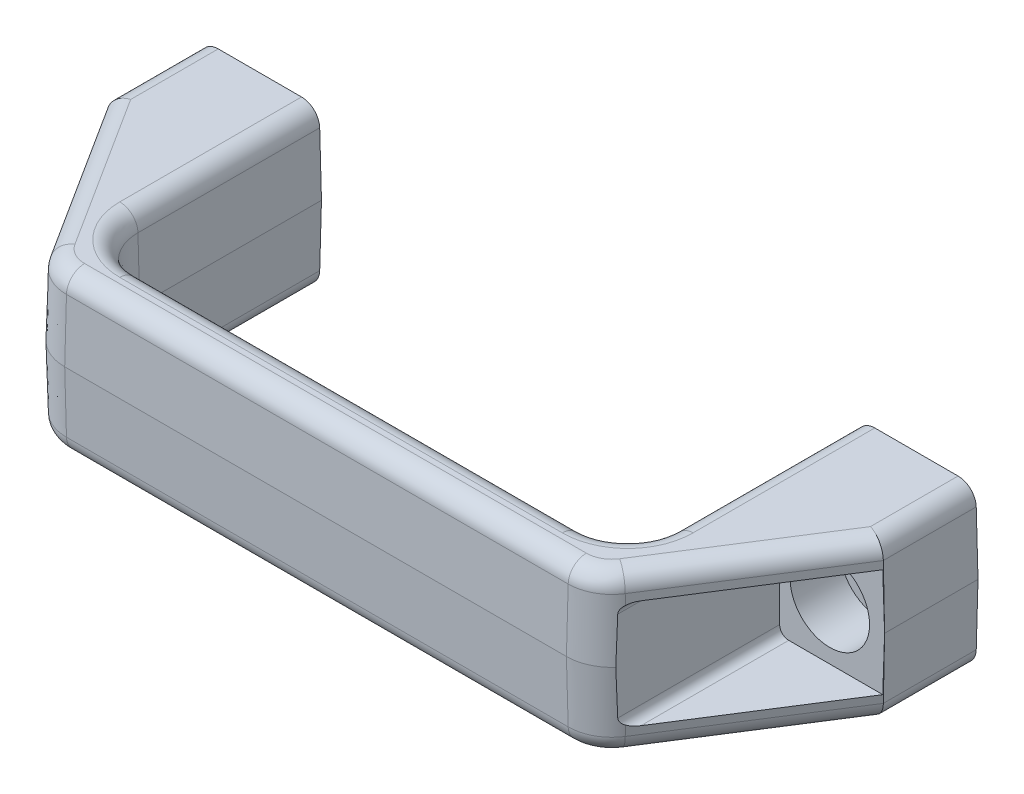
SolidWorks part; units mm, degrees
ref_plane "Front Plane" through (0, 0, 0) normal (0, 0, 1) x (1, 0, 0)
ref_plane "Top Plane" through (0, 0, 0) normal (0, 1, 0) x (1, 0, 0)
ref_plane "Right Plane" through (0, 0, 0) normal (1, 0, 0) x (0, 0, -1)
sketch "Sketch1" plane through (0, 0, 0) normal (0, 0, 1) x (1, 0, 0)
  line L0 (-46.8312, 0) -> (46.8312, 0)
  line L1 (0, 11.1125) -> (0, -11.1125)
  line L2 (-3, -11.1125) -> (3, -11.1125)
  point P4 (0, 0)
  point P8 (0, 0)
  point P10 (0, -11.1125)
sketch "Sketch2" plane through (0, 0, 0) normal (0, 1, 0) x (1, 0, 0)
  line L0 (0, 0) -> (0, -38.1)
  line L1 (0, -38.1) -> (0, -31.75)
  line L2 (-54.483, 0) -> (54.483, 0)
  point P7 (0, 0)
sketch "Sketch3" plane through (0, 0, 0) normal (0, 1, 0) x (1, 0, 0)
  line L0 (-30.9253, -31.75) -> (30.9253, -31.75)
  line L1 (37.2752, -25.4) -> (37.2752, 0)
  line L2 (-46.8312, 0) -> (46.8312, 0) construction
  line L3 (37.2752, 0) -> (54.483, 0)
  line L4 (54.483, 0) -> (54.483, -13.0556)
  line L5 (54.483, -13.0556) -> (40.4167, -35.1592)
  line L6 (35.0595, -38.1) -> (-35.0595, -38.1)
  line L7 (-40.4167, -35.1592) -> (-54.483, -13.0556)
  line L8 (-54.483, -13.0556) -> (-54.483, 0)
  line L9 (-54.483, 0) -> (-37.2752, 0)
  line L10 (-37.2752, 0) -> (-37.2752, -25.4)
  line L11 (0, 0) -> (0, -31.75) construction
  arc A0 (37.2752, -25.4) -> (30.9253, -31.75) centre (30.9253, -25.4) cw
  arc A1 (-30.9253, -31.75) -> (-37.2752, -25.4) centre (-30.9253, -25.4) cw
  arc A2 (-35.0595, -38.1) -> (-40.4167, -35.1592) centre (-35.0595, -31.75) cw
  arc A3 (35.0595, -38.1) -> (40.4167, -35.1592) centre (35.0595, -31.75) ccw
  point P17 (37.2752, -31.75)
  point P20 (-37.2752, -31.75)
  point P23 (-38.5453, -38.1)
  point P26 (38.5452, -38.1)
  dimension "D11" = 6.35
  dimension "D12" = 6.35
  dimension "D13" = 6.35
  dimension "D1" = 38.1
  dimension "D2" = 6.35
  dimension "D5" = 1.27
  dimension "D6" = 1.27
  dimension "D7" = 13.0556
  dimension "D8" = 13.0556
  dimension "D3" = 74.5505
extrude "Boss-Extrude1" add sketch "Sketch3" along normal up to vertex (11.1125 mm away) from vertex at -11.1125 starting at point (0, -11.1125, 0)
sketch "Sketch4" plane through (0, 0, 0) normal (1, 0, 0) x (0, 0, -1)
  line L0 (-38.1, 0) -> (-37.7825, 11.1125)
  line L1 (-38.1, 11.1125) -> (-38.1, -11.1125) construction
  line L2 (-35.1592, 11.1125) -> (-38.1, 11.1125) construction
  line L5 (-37.7825, 11.1125) -> (-38.1, 11.1125)
  line L6 (-38.1, 11.1125) -> (-38.1, 0)
  dimension "D1" = 0.3175
sketch "Sketch5" plane through (0, 0, 0) normal (0, 1, 0) x (1, 0, 0)
  line L0 (-54.483, 0) -> (-54.483, -13.0556)
  line L1 (54.483, -13.0556) -> (40.4167, -35.1592)
  line L2 (54.483, 0) -> (54.483, -13.0556)
  line L3 (-54.483, -13.0556) -> (-40.4167, -35.1592)
  line L4 (-35.0595, -38.1) -> (35.0595, -38.1)
  arc A0 (35.0595, -38.1) -> (40.4167, -35.1592) centre (35.0595, -31.75) ccw
  arc A1 (-35.0595, -38.1) -> (-40.4167, -35.1592) centre (-35.0595, -31.75) cw
  dimension "D4" = 13.0556
sweep "Cut-Sweep1" cut profiles "Sketch4" path "Sketch5"
mirror "Mirror1" about plane through (0, 0, 0) normal (0, 1, 0) of "Cut-Sweep1"
ref_plane "Plane1" through (0, 0, 13.0556) normal (0, 0, 1) x (1, 0, 0)
sketch "Sketch6" plane through (0, 0, 13.0556) normal (0, 0, 1) x (1, 0, 0)
  line L1 (-54.483, 7.5565) -> (-41.0853, 7.5565)
  line L2 (-54.483, 7.5565) -> (-54.483, -7.5565)
  line L3 (-54.483, -7.5565) -> (-41.0853, -7.5565)
  line L4 (-39.8152, 6.2865) -> (-39.8152, -6.2865)
  line L7 (54.1655, 11.1125) -> (37.2752, 11.1125) construction
  line L8 (54.483, 7.5565) -> (41.0852, 7.5565)
  line L9 (54.483, 7.5565) -> (54.483, -7.5565)
  line L10 (54.483, -7.5565) -> (41.0853, -7.5565)
  line L11 (39.8152, 6.2865) -> (39.8153, -6.2865)
  line L12 (54.1655, -11.1125) -> (37.2752, -11.1125) construction
  line L13 (37.2752, 11.1125) -> (37.2752, -11.1125) construction
  arc A0 (41.0852, 7.5565) -> (39.8152, 6.2865) centre (41.0852, 6.2865) ccw
  arc A1 (39.8153, -6.2865) -> (41.0853, -7.5565) centre (41.0852, -6.2865) ccw
  arc A2 (-39.8152, -6.2865) -> (-41.0853, -7.5565) centre (-41.0852, -6.2865) cw
  arc A3 (-39.8152, 6.2865) -> (-41.0853, 7.5565) centre (-41.0852, 6.2865) ccw
  dimension "D3" = 1.27
  dimension "D4" = 3.556
  dimension "D5" = 3.556
  dimension "D6" = 2.54
  dimension "D1" = 39.8152
  dimension "D2" = 15.113
extrude "Cut-Extrude1" cut sketch "Sketch6" along normal through all
sketch "Sketch7" plane through (0, 0, 0) normal (0, 0, 1) x (1, 0, 0)
  circle A0 centre (-46.8312, 0) radius 3
  circle A1 centre (46.8312, 0) radius 3
  dimension "D1" = 6
  dimension "D2" = 6
extrude "Cut-Extrude2" cut sketch "Sketch7" along normal through all
sketch "Sketch8" plane through (0, 0, 13.0556) normal (0, 0, 1) x (1, 0, 0)
  circle A0 centre (-46.8312, 0) radius 5.55
  circle A1 centre (46.8312, 0) radius 5.55
  dimension "D1" = 11.1
  dimension "D2" = 11.1
extrude "Cut-Extrude3" cut sketch "Sketch8" against normal blind 6.985
sketch "Sketch9" plane through (0, 0, 0) normal (1, 0, 0) x (0, 0, -1)
  line L0 (-31.75, 11.1125) -> (-31.75, 0)
  line L1 (-38.1, 0) -> (-31.75, 0) construction
  line L2 (-31.75, 0) -> (-32.0675, 11.1125)
  line L3 (-12.9631, 11.1125) -> (-34.9888, 11.1125) construction
  line L4 (-32.0675, 11.1125) -> (-31.75, 11.1125)
  dimension "D1" = 0.3175
sketch "Sketch10" plane through (0, 0, 0) normal (0, 1, 0) x (1, 0, 0)
  line L0 (-37.2752, 0) -> (-37.2752, -25.4)
  line L1 (37.2752, 0) -> (37.2752, -25.4)
  line L2 (-30.9253, -31.75) -> (30.9253, -31.75)
  arc A0 (-37.2752, -25.4) -> (-30.9253, -31.75) centre (-30.9253, -25.4) ccw
  arc A1 (30.9253, -31.75) -> (37.2752, -25.4) centre (30.9252, -25.4) ccw
sweep "Cut-Sweep2" cut profiles "Sketch9" path "Sketch10"
mirror "Mirror2" about plane through (0, 0, 0) normal (0, 1, 0) of "Cut-Sweep2"
sketch "Sketch11" plane through (0, 0, 0) normal (0, 0, 1) x (1, 0, 0)
  line L0 (54.483, 0) -> (37.2752, 0) construction
  line L1 (-37.2752, 0) -> (-54.483, 0) construction
  line L2 (-39.9643, 5.1814) -> (-40.0436, 7.9556)
  line L3 (-37.5927, 11.1125) -> (-37.2752, 0) construction
  line L11 (40.0612, 8.5725) -> (39.8142, -0.0725)
  line L12 (51.697, 8.5725) -> (40.0612, 8.5725)
  line L13 (51.944, -0.0725) -> (51.697, 8.5725)
  line L14 (40.0436, 7.9556) -> (39.9643, 5.1814)
  line L15 (51.0799, 8.5725) -> (40.6783, 8.5725)
  line L16 (51.7939, 5.1814) -> (51.7147, 7.9556)
  line L23 (40.0612, -8.5725) -> (39.8142, 0.0725)
  line L25 (51.697, -8.5725) -> (40.0612, -8.5725)
  line L26 (51.944, 0.0725) -> (51.697, -8.5725)
  line L27 (40.0436, -7.9556) -> (39.9643, -5.1814)
  line L28 (51.0799, -8.5725) -> (40.6783, -8.5725)
  line L29 (51.7939, -5.1814) -> (51.7147, -7.9556)
  line L54 (-51.942, 0) -> (-51.697, -8.5725)
  line L55 (-51.697, 8.5725) -> (-51.942, 0)
  line L56 (-40.0612, 8.5725) -> (-51.697, 8.5725)
  line L57 (-39.8163, 0) -> (-40.0612, 8.5725)
  line L58 (-40.0612, -8.5725) -> (-39.8163, 0)
  line L59 (-51.697, -8.5725) -> (-40.0612, -8.5725)
  line L60 (-51.7939, -5.1814) -> (-51.7147, -7.9556)
  line L61 (-51.7147, 7.9556) -> (-51.7939, 5.1814)
  line L62 (-40.6783, 8.5725) -> (-51.0799, 8.5725)
  line L64 (-40.0436, -7.9556) -> (-39.9643, -5.1814)
  line L65 (-51.0799, -8.5725) -> (-40.6783, -8.5725)
  arc A0 (50.7052, 4.7193) -> (41.0531, 4.7193) centre (45.8791, 0) ccw
  arc A1 (-50.7052, -4.7193) -> (-41.0531, -4.7193) centre (-45.8791, 0) ccw
  arc A2 (41.0531, -4.7193) -> (50.7052, -4.7193) centre (45.8791, 0) ccw
  arc A4 (-41.0531, 4.7193) -> (-50.7052, 4.7193) centre (-45.8791, 0) ccw
  arc A5 (-40.0436, -7.9556) -> (-40.6783, -8.5725) centre (-40.6783, -7.9375) cw
  arc A6 (-51.0799, -8.5725) -> (-51.7147, -7.9556) centre (-51.0799, -7.9375) cw
  arc A7 (-51.7939, -5.1814) -> (-50.7052, -4.7193) centre (-51.1592, -5.1633) cw
  arc A8 (-41.0531, -4.7193) -> (-39.9643, -5.1814) centre (-40.5991, -5.1633) cw
  arc A9 (-50.7052, 4.7193) -> (-51.7939, 5.1814) centre (-51.1592, 5.1633) cw
  arc A10 (-51.7147, 7.9556) -> (-51.0799, 8.5725) centre (-51.0799, 7.9375) cw
  arc A11 (-40.6783, 8.5725) -> (-40.0436, 7.9556) centre (-40.6783, 7.9375) cw
  arc A12 (-39.9643, 5.1814) -> (-41.0531, 4.7193) centre (-40.5991, 5.1633) cw
  arc A13 (50.7052, -4.7193) -> (51.7939, -5.1814) centre (51.1592, -5.1633) cw
  arc A14 (51.7147, -7.9556) -> (51.0799, -8.5725) centre (51.0799, -7.9375) cw
  arc A15 (40.6783, -8.5725) -> (40.0436, -7.9556) centre (40.6783, -7.9375) cw
  arc A16 (39.9643, -5.1814) -> (41.0531, -4.7193) centre (40.5991, -5.1633) cw
  arc A17 (41.0531, 4.7193) -> (39.9643, 5.1814) centre (40.5991, 5.1633) cw
  arc A18 (40.0436, 7.9556) -> (40.6783, 8.5725) centre (40.6783, 7.9375) cw
  arc A19 (51.0799, 8.5725) -> (51.7147, 7.9556) centre (51.0799, 7.9375) cw
  arc A20 (50.7052, 4.7193) -> (51.7939, 5.1814) centre (51.1592, 5.1633) ccw
  dimension "D1" = 13.5
  dimension "D2" = 13.5
  dimension "D9" = 0.635
  dimension "D7" = 6.75
  dimension "D6" = 37.2752
  dimension "D8" = 2.54
  dimension "D3" = 2.54
  dimension "D4" = 2.54
  dimension "D5" = 2.54
extrude "Cut-Extrude4" cut sketch "Sketch11" along normal blind 10.5156
fillet "Fillet1" radius 2.54 24 edges at (-47.1572, 11.1125, 23.976) (-37.9624, 11.1125, 37.0381) (0, 11.1125, 37.7825) (37.9624, 11.1125, 37.0381) (-47.1572, -11.1125, 23.976) (-37.9624, -11.1125, 37.0381) (0, -11.1125, 37.7825) (37.9624, -11.1125, 37.0381) (37.5927, -11.1125, 12.7) (35.6399, -11.1125, 30.1146) (-37.5927, -11.1125, 12.7) (-35.6399, -11.1125, 30.1146) (37.5927, 11.1125, 12.7) (35.6399, 11.1125, 30.1146) (-37.5927, 11.1125, 12.7) (-35.6399, 11.1125, 30.1146) (-54.1655, -11.1125, 6.4816) (-54.1655, 11.1125, 6.4816) (47.1572, 11.1125, 23.976) (47.1572, -11.1125, 23.976) (54.1655, -11.1125, 6.4816) (54.1655, 11.1125, 6.4816) (0, -11.1125, 32.0675) (0, 11.1125, 32.0675)
equation "\"D1@Sketch3\"=\"Projection@Sketch2\""
equation "\"D2@Sketch6\"=\"Height@Sketch1\"-.28"
equation "\"D1@Sketch7\"=\"Screw Size@Sketch1\""
equation "\"D2@Sketch7\"=\"Screw Size@Sketch1\""
equation "\"D1@Sketch8\"=\"Screw Size@Sketch1\"*1.85"
equation "\"D2@Sketch8\"=\"Screw Size@Sketch1\"*1.85"
equation "\"D3@Sketch3\"=\"Mt Hole Ctr to Ctr Width@Sketch1\"-\"Screw Size@Sketch1\"*2-.28"
equation "\"D1@Sketch6\"=(\"D3@Sketch3\"/2)+.1"
equation "\"D1@Sketch11\"=\"Screw Size@Sketch1\"*2.25"
equation "\"D2@Sketch11\"=\"Screw Size@Sketch1\"*2.25"
equation "\"D6@Sketch11\"=(\"Mt Hole Ctr to Ctr Width@Sketch1\"-\"Screw Size@Sketch1\"*2-.28)/2"
equation "\"D7@Sketch11\"=\"Screw Size@Sketch1\"*1.125"
